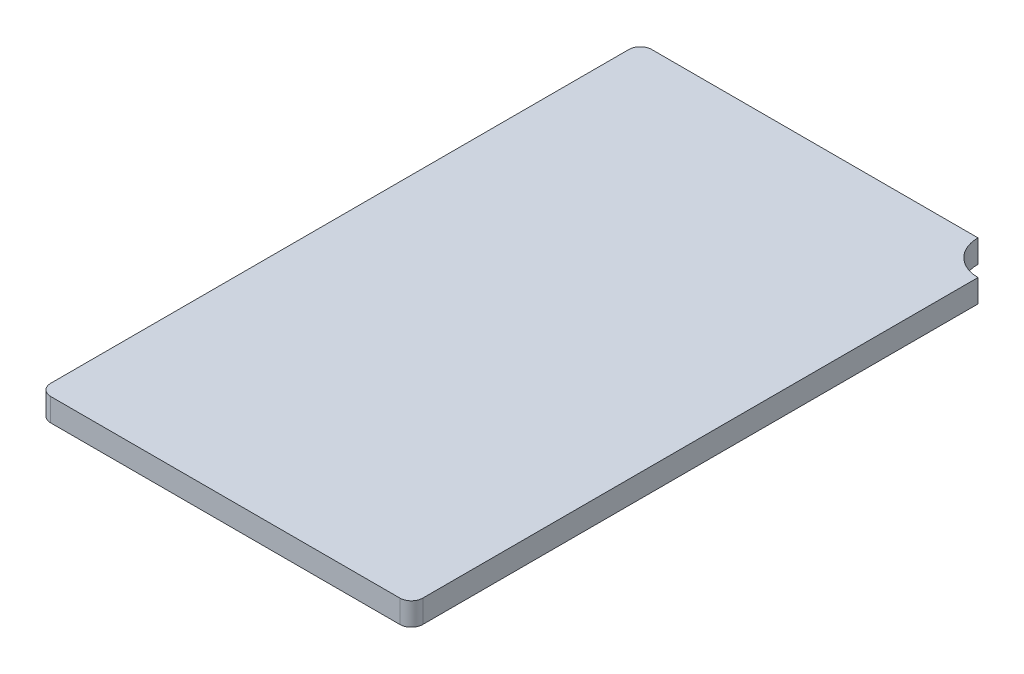
SolidWorks part; units mm, degrees
ref_plane "Front Plane" through (0, 0, 0) normal (0, 0, 1) x (1, 0, 0)
ref_plane "Top Plane" through (0, 0, 0) normal (0, 1, 0) x (1, 0, 0)
ref_plane "Right Plane" through (0, 0, 0) normal (1, 0, 0) x (0, 0, -1)
sketch "Sketch1" plane through (0, 0, 0) normal (0, 1, 0) x (1, 0, 0)
  line L1 (-1.625, 2.625) -> (1.625, 2.625)
  line L2 (-1.625, 2.625) -> (-1.625, -2.625)
  line L3 (-1.625, -2.625) -> (1.625, -2.625)
  line L4 (1.625, 2.625) -> (1.625, -2.625)
  line L5 (-1.625, 2.625) -> (1.625, -2.625) construction
  line L6 (-1.625, -2.625) -> (1.625, 2.625) construction
  point P0 (0, 0)
  dimension "D1" = 3.25
  dimension "D2" = 5.25
extrude "Boss-Extrude1" add sketch "Sketch1" along normal blind 0.2
sketch "Sketch2" plane through (0, 0.2, 0) normal (0, 1, 0) x (1, 0, 0)
  circle A0 centre (1.625, 2.625) radius 0.3
  dimension "D1" = 0.6
extrude "Cut-Extrude1" cut sketch "Sketch2" against normal through all
fillet "Fillet1" radius 0.1 3 edges at (1.625, 0.1, 2.625) (-1.625, 0.1, 2.625) (-1.625, 0.1, -2.625)
